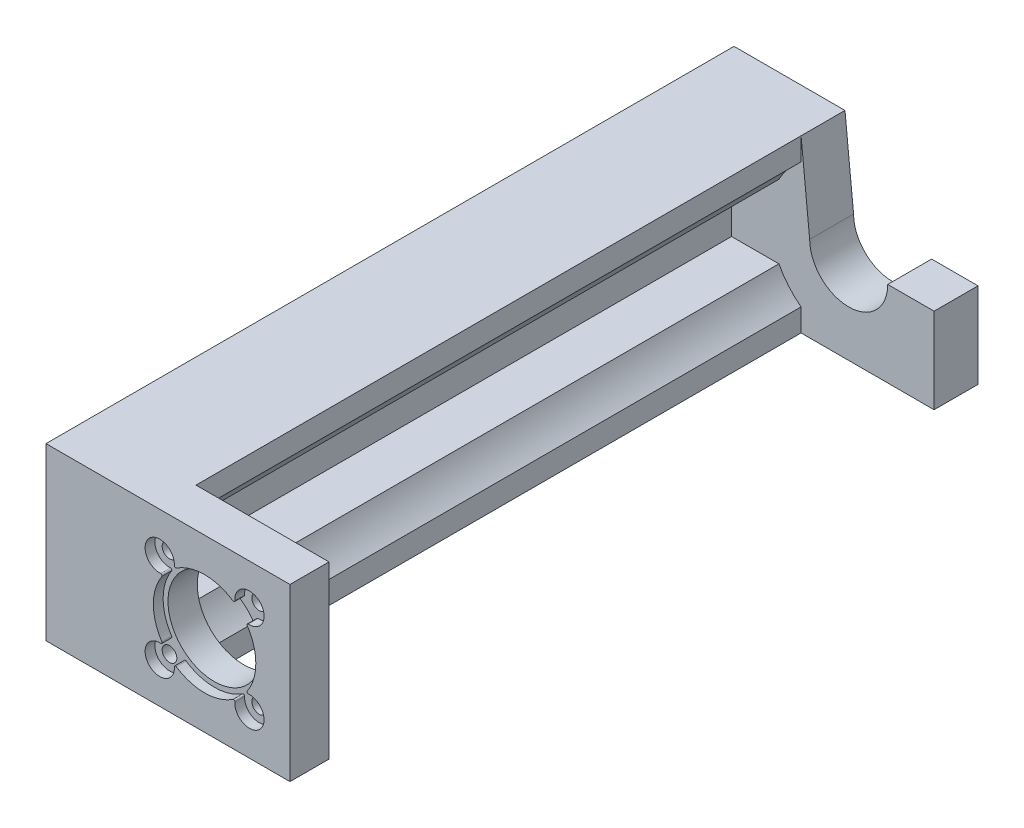
SolidWorks part; units mm, degrees
ref_plane "Piano frontale" through (0, 0, 0) normal (0, 0, 1) x (1, 0, 0)
ref_plane "Piano superiore" through (0, 0, 0) normal (0, 1, 0) x (1, 0, 0)
ref_plane "Piano destro" through (0, 0, 0) normal (1, 0, 0) x (0, 0, -1)
sketch "Sketch1" plane through (0, 0, 0) normal (0, 0, 1) x (1, 0, 0)
  line L0 (0, 17.5) -> (50, 17.5) construction
  line L1 (0, 0) -> (50, 0)
  line L2 (0, 0) -> (0, 35)
  line L3 (0, 35) -> (50, 35)
  line L4 (50, 0) -> (50, 35)
  line L5 (25, 35) -> (25, 0) construction
  line L6 (32.5, 17.5) -> (41.6924, 26.6924) construction
  line L7 (32.5, 17.5) -> (41.6924, 8.3076) construction
  line L8 (32.5, 17.5) -> (32.5, 0) construction
  line L9 (32.5, 17.5) -> (23.3076, 8.3076) construction
  line L10 (32.5, 17.5) -> (23.3076, 26.6924) construction
  circle A0 centre (32.5, 17.5) radius 9.5
  circle A1 centre (32.5, 17.5) radius 13 construction
  circle A2 centre (41.6924, 26.6924) radius 1.5
  circle A3 centre (41.6924, 8.3076) radius 1.5
  circle A4 centre (23.3076, 8.3076) radius 1.5
  circle A5 centre (23.3076, 26.6924) radius 1.5
  circle A6 centre (32.5, 17.5) radius 16 construction
  dimension "D2" = 19
  dimension "D4" = 26
  dimension "D6" = 3
  dimension "D7" = 17.5
  dimension "D9" = 32
  dimension "D1" = 50
  dimension "D3" = 17.5
  dimension "D5" = 45
  dimension "D8" = 35
extrude "Boss-Extrude3" add sketch "Sketch1" along normal blind 6
sketch "Sketch4" plane through (0, 0, 6) normal (0, 0, 1) x (1, 0, 0)
  line L0 (32.5, 17.5) -> (32.5, 34.7569) construction
  line L1 (32.5, 17.5) -> (32.5, 0) construction
  line L2 (0, 0) -> (50, 0) construction
  line L3 (32.5, 17.5) -> (0, 17.5) construction
  line L4 (0, 35) -> (0, 0) construction
  line L6 (0, 35) -> (50, 35)
  line L7 (0, 35) -> (0, 0)
  line L8 (0, 0) -> (50, 0)
  line L9 (50, 35) -> (50, 0)
  arc A0 (26.2994, 26.4708) -> (23.5292, 23.7006) centre (23.3076, 26.6924) ccw
  arc A1 (26.2994, 8.5292) -> (23.5292, 11.2994) centre (23.3076, 8.3076) cw
  arc A2 (38.7006, 8.5292) -> (41.4708, 11.2994) centre (41.6924, 8.3076) ccw
  arc A3 (38.7006, 26.4708) -> (41.4708, 23.7006) centre (41.6924, 26.6924) cw
  arc A4 (23.7558, 23.3129) -> (23.7558, 11.6871) centre (32.5, 17.5) ccw
  arc A5 (38.3129, 26.2442) -> (26.6871, 26.2442) centre (32.5, 17.5) ccw
  arc A6 (41.2442, 11.6871) -> (41.2442, 23.3129) centre (32.5, 17.5) ccw
  arc A7 (26.6871, 8.7558) -> (38.3129, 8.7558) centre (32.5, 17.5) ccw
  arc A8 (23.7558, 11.6871) -> (23.5292, 11.2994) centre (23.5476, 11.5487) cw
  arc A9 (26.6871, 8.7558) -> (26.2994, 8.5292) centre (26.5487, 8.5476) ccw
  arc A10 (38.3129, 8.7558) -> (38.7006, 8.5292) centre (38.4513, 8.5476) cw
  arc A11 (41.2442, 11.6871) -> (41.4708, 11.2994) centre (41.4524, 11.5487) ccw
  arc A12 (41.2442, 23.3129) -> (41.4708, 23.7006) centre (41.4524, 23.4513) cw
  arc A13 (38.3129, 26.2442) -> (38.7006, 26.4708) centre (38.4513, 26.4524) ccw
  arc A14 (26.6871, 26.2442) -> (26.2994, 26.4708) centre (26.5487, 26.4524) cw
  arc A15 (23.7558, 23.3129) -> (23.5292, 23.7006) centre (23.5476, 23.4513) ccw
  dimension "D1" = 6
  dimension "D2" = 21
  dimension "D3" = 0.25
extrude "Boss-Extrude5" add sketch "Sketch4" along normal blind 2
sketch "Sketch8" plane through (0, 0, 0) normal (0, 0, -1) x (-1, 0, 0)
  line L0 (-50, 35) -> (0, 35) construction
  line L1 (-22.7403, 35) -> (0, 35)
  line L2 (-22.7403, 35) -> (-22.7403, 30.3675)
  line L3 (-22.7403, 0) -> (0, 0)
  line L4 (0, 35) -> (0, 0)
  line L5 (-22.7403, 4.6325) -> (-22.7403, 0)
  line L6 (0, 35) -> (0, 0) construction
  line L7 (-16.35, 17.5) -> (-32.5, 17.5) construction
  line L8 (-8.5, 25) -> (-18.1947, 25)
  line L9 (0, 25) -> (0, 10)
  line L10 (-8.5, 10) -> (-18.1971, 10)
  line L11 (-18.1947, 25) -> (-18.1947, 24.9954)
  line L13 (0, 35) -> (-8.5, 35)
  line L14 (0, 35) -> (0, 0)
  line L15 (0, 0) -> (-8.5, 0)
  line L16 (-8.5, 25) -> (-8.5, 10)
  arc A0 (-22.7403, 4.6325) -> (-18.1971, 10) centre (-32.5, 17.5) ccw
  arc A1 (-18.1947, 24.9954) -> (-22.7403, 30.3675) centre (-32.5, 17.5) ccw
  line M3 (0, 0) -> (0, 35)
  line M4 (0, 35) -> (-50, 35)
  line M6 (-50, 0) -> (0, 0)
  dimension "D1" = 32.3
  dimension "D2" = 22.7403
  dimension "D3" = 15
  dimension "D4" = 18.1947
  dimension "D5" = 25
  dimension "D6" = 8.5
extrude "Boss-Extrude6" add sketch "Sketch8" along normal blind 124 contours A1 L11 L8 L16 L10 A0 L5 L3 L4 L1 L2 M6 M3 M4
sketch "Sketch9" plane through (0, 0, 0) normal (-1, 0, 0) x (0, 0, 1)
  line L0 (-124, 17.5) -> (8, 17.5) construction
  line L1 (-124, 0) -> (-124, 35) construction
  line L2 (8, 35) -> (8, 0) construction
  line L3 (-141, 17.5) -> (-9, 17.5) construction
  line L4 (-158, 17.5) -> (-26, 17.5) construction
  line L5 (-175, 17.5) -> (-43, 17.5) construction
  line L6 (-192, 17.5) -> (-60, 17.5) construction
  line L7 (-209, 17.5) -> (-77, 17.5) construction
  line L8 (-226, 17.5) -> (-94, 17.5) construction
  line L9 (-243, 17.5) -> (-111, 17.5) construction
  circle A0 centre (-7, 17.5) radius 2
  circle A1 centre (-24, 17.5) radius 2
  circle A2 centre (-41, 17.5) radius 2
  circle A3 centre (-58, 17.5) radius 2
  circle A4 centre (-75, 17.5) radius 2
  circle A5 centre (-92, 17.5) radius 2
  circle A6 centre (-109, 17.5) radius 2
  circle A8 centre (-126, 17.5) radius 2 [skipped]
  dimension "D1" = 4
  dimension "D2" = 15
  dimension "D3" = 8
extrude "Cut-Extrude1" cut sketch "Sketch9" against normal blind 115
sketch "Sketch12" plane through (0, 0, -124) normal (0, 0, -1) x (-1, 0, 0)
  line L0 (-24.5, 17.5) -> (-22.7403, 35)
  line L5 (-50, 35) -> (-22.7403, 35) construction
  line L6 (-22.7403, 35) -> (0, 35)
  line L8 (-50, 0) -> (0, 0)
  line L9 (0, 35) -> (0, 0)
  line L11 (-22.7403, 0) -> (-50, 0) construction
  line L12 (-50, 0) -> (-50, 17.5)
  line L13 (-50, 0) -> (-50, 35) construction
  line L14 (-50, 17.5) -> (-40.5, 17.5)
  arc A1 (-40.5, 17.5) -> (-24.5, 17.5) centre (-32.5, 17.5) ccw
  dimension "D2" = 16
extrude "Boss-Extrude7" add sketch "Sketch12" along normal blind 9
